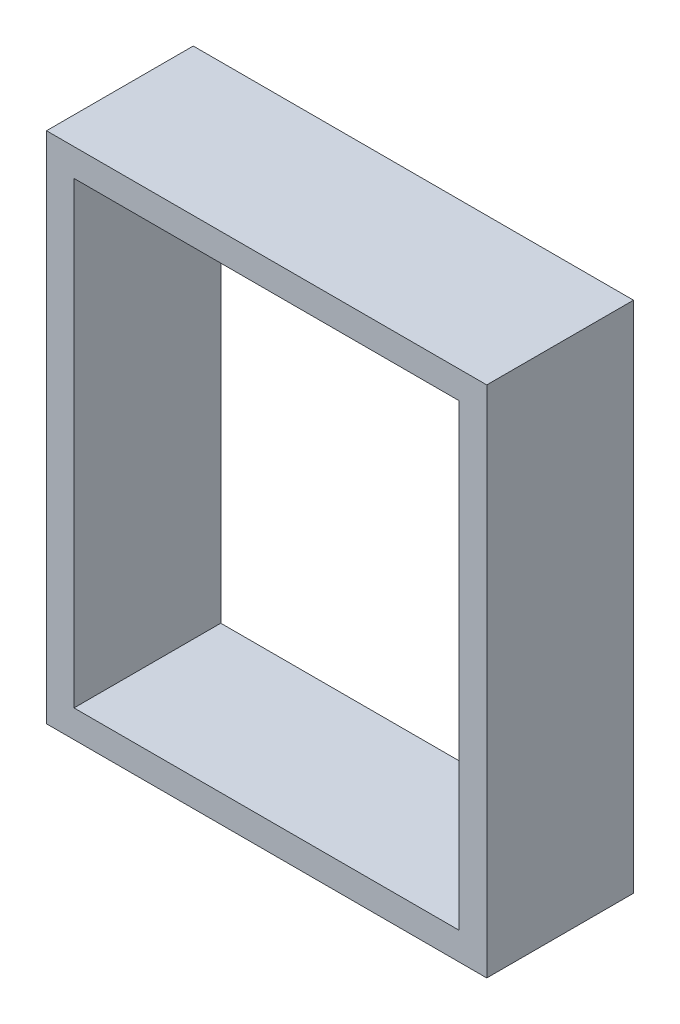
SolidWorks part; units mm, degrees
ref_plane "Front Plane" through (0, 0, 0) normal (0, 0, 1) x (1, 0, 0)
ref_plane "Top Plane" through (0, 0, 0) normal (0, 1, 0) x (1, 0, 0)
ref_plane "Right Plane" through (0, 0, 0) normal (1, 0, 0) x (0, 0, -1)
sketch "Sketch1" plane through (0, 0, 0) normal (0, 0, 1) x (1, 0, 0)
  line L0 (-33.3375, 39.6875) -> (33.3375, 39.6875)
  line L1 (-38.1, 44.45) -> (38.1, 44.45)
  line L2 (-38.1, 44.45) -> (-38.1, -44.45)
  line L3 (-38.1, -44.45) -> (38.1, -44.45)
  line L4 (38.1, 44.45) -> (38.1, -44.45)
  line L5 (33.3375, 39.6875) -> (33.3375, -39.6875)
  line L6 (-33.3375, -39.6875) -> (33.3375, -39.6875)
  line L7 (-33.3375, 39.6875) -> (-33.3375, -39.6875)
  dimension "D1" = 88.9
  dimension "D2" = 76.2
  dimension "D3" = 38.1
  dimension "D4" = 44.45
  dimension "D5" = 4.7625
extrude "Boss-Extrude1" add sketch "Sketch1" along normal blind 25.4
equation "\"D3@Sketch1\"=\"D2@Sketch1\"/2"
equation "\"D4@Sketch1\"=\"D1@Sketch1\"/2"
